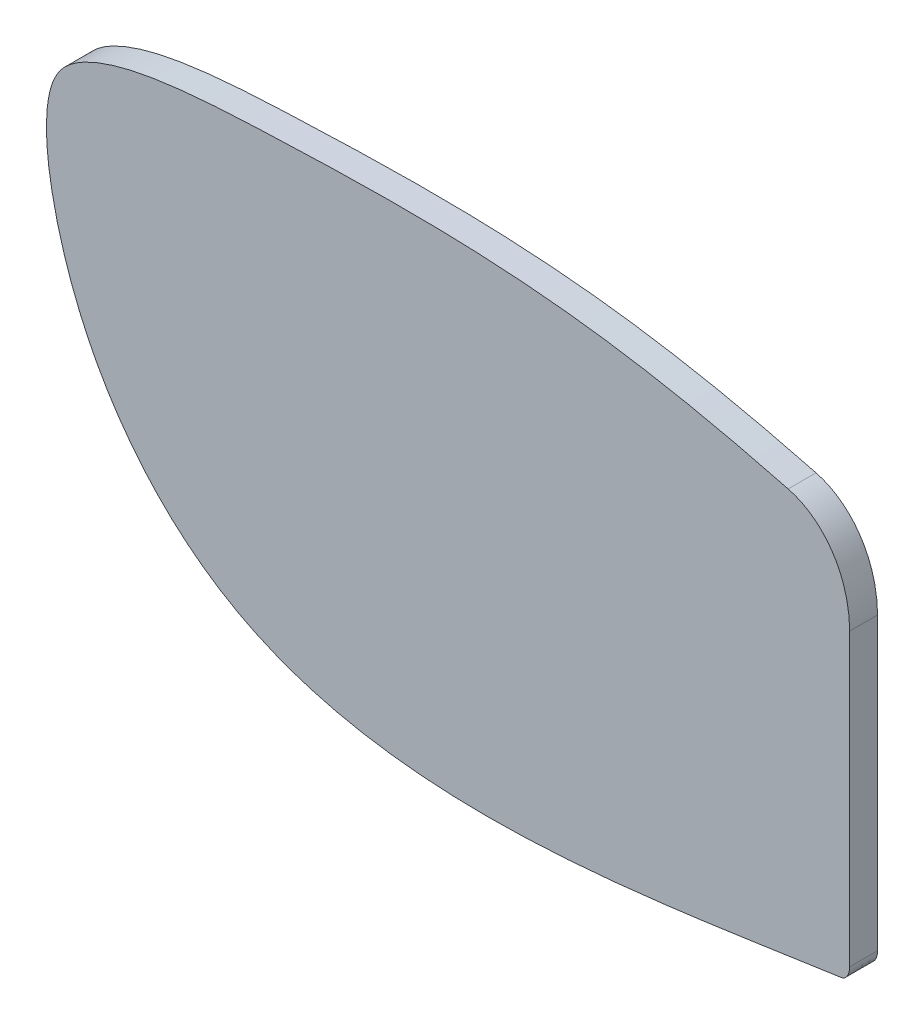
SolidWorks part; units mm, degrees
material "Glass"
ref_plane "Front Plane" through (0, 0, 0) normal (0, 0, 1) x (1, 0, 0)
ref_plane "Top Plane" through (0, 0, 0) normal (0, 1, 0) x (1, 0, 0)
ref_plane "Right Plane" through (0, 0, 0) normal (1, 0, 0) x (0, 0, -1)
sketch "Sketch1" plane through (0, 0, 0) normal (0, 0, 1) x (1, 0, 0)
  line L1 (-34.3449, 22.453) -> (-34.3449, 12.0213)
  spline S6 degree 3 poles (-34.6405, 11.5409) (-35.2172, 11.4588) (-36.3389, 11.2932) (-38.2069, 11.0154) (-40.1635, 10.7409) (-42.8458, 10.4135) (-46.2297, 10.1428) (-50.2721, 10.2232) (-53.6081, 10.8541) (-56.1228, 11.9049) (-57.8333, 12.9984) (-59.3571, 14.3915) (-60.6711, 16.0539) (-61.7229, 17.8967) (-62.5162, 19.8974) (-63.0433, 21.9763) (-63.2251, 23.7438) (-63.0307, 25.097) (-62.6222, 25.8767) (-61.8401, 26.4238) (-60.5911, 26.9172) (-58.8861, 27.2348) (-56.8202, 27.4044) (-54.7215, 27.4904) (-51.9382, 27.5843) (-48.4913, 27.6041) (-44.3807, 27.3366) (-41.0152, 26.803) (-38.3947, 26.2327) (-37.172, 25.9281) (-36.5528, 25.7662) knots 0 0 0 0 0.03125 0.0625 0.09375 0.125 0.1875 0.25 0.3125 0.34375 0.375 0.40625 0.4375 0.46875 0.5 0.53125 0.5625 0.578125 0.59375 0.609375 0.625 0.65625 0.6875 0.71875 0.75 0.8125 0.875 0.9375 0.96875 1 1 1 1
  spline S7 degree 3 poles (-36.5528, 25.7662) (-36.2469, 25.6863) (-35.6682, 25.4156) (-34.9577, 24.6941) (-34.4652, 23.6831) (-34.3449, 22.8543) (-34.3449, 22.453) knots 0 0 0 0 0.25 0.5 0.75 1 1 1 1
  spline S8 degree 3 poles (-34.3449, 12.0213) (-34.3449, 11.9509) (-34.3694, 11.801) (-34.4569, 11.6457) (-34.5561, 11.5635) (-34.6098, 11.5453) (-34.6405, 11.5409) knots 0 0 0 0 0.25 0.5 0.75 1 1 1 1
extrude "Boss-Extrude1" add sketch "Sketch1" along normal blind 1
